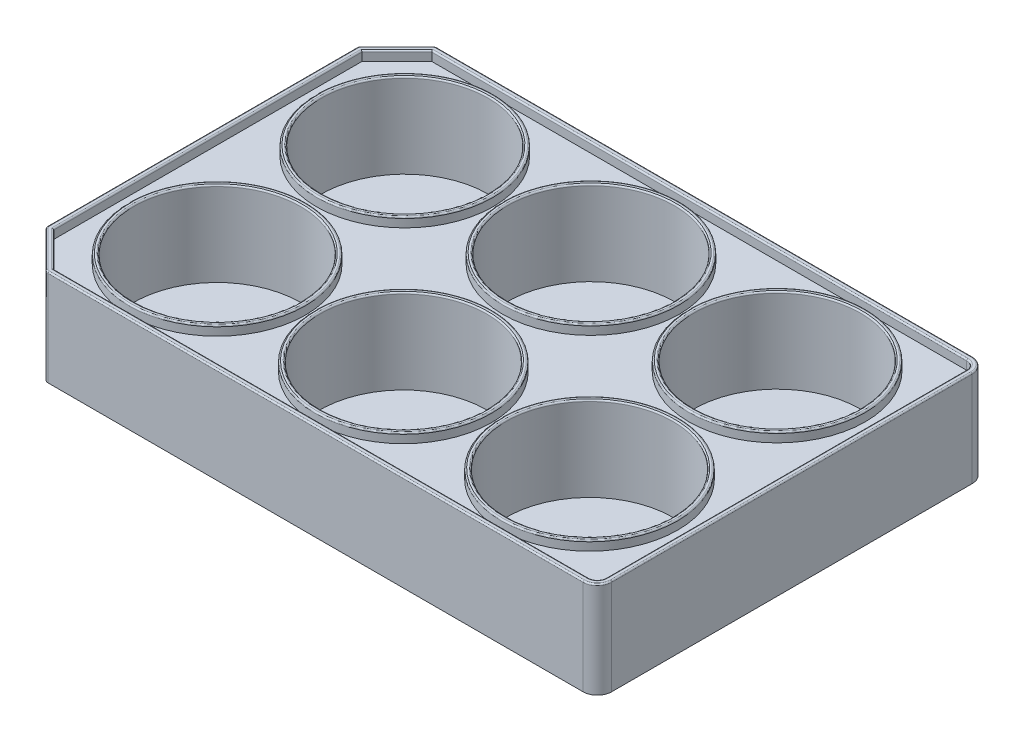
SolidWorks part; units mm, degrees
ref_plane "Front Plane" through (0, 0, 0) normal (0, 0, 1) x (1, 0, 0)
ref_plane "Top Plane" through (0, 0, 0) normal (0, 1, 0) x (1, 0, 0)
ref_plane "Right Plane" through (0, 0, 0) normal (1, 0, 0) x (0, 0, -1)
sketch "Sketch1" plane through (0, 0, 0) normal (0, 1, 0) x (1, 0, 0)
  line L1 (0, 0) -> (123.5, 0)
  line L2 (0, 0) -> (0, -81.5)
  line L3 (0, -81.5) -> (123.5, -81.5)
  line L4 (123.5, 0) -> (123.5, -81.5)
  dimension "D1" = 123.5
  dimension "D2" = 81.5
extrude "Boss-Extrude1" add sketch "Sketch1" along normal blind 20.16
chamfer "Chamfer1" distance 8 angle 45 2 edges at (0, 10.08, 0) (0, 10.08, 81.5)
fillet "Fillet1" radius 1 4 edges at (8, 10.08, 0) (0, 10.08, 8) (8, 10.08, 81.5) (0, 10.08, 73.5)
sketch "Sketch2" plane through (0, 20.16, 0) normal (0, 1, 0) x (1, 0, 0)
  line L0 (0, -8.4142) -> (0, -73.0858) construction
  line L1 (123.5, 0) -> (8.4142, 0) construction
  circle A0 centre (22.75, -21.1) radius 17.5
  circle A1 centre (61.75, -21.1) radius 17.5
  circle A2 centre (100.75, -21.1) radius 17.5
  circle A3 centre (61.75, -60.4) radius 17.5
  circle A4 centre (100.75, -60.4) radius 17.5
  circle A5 centre (22.75, -60.4) radius 17.5
  dimension "D2" = 35
  dimension "D3" = 21.1
  dimension "D1" = 22.75
  dimension "D4" = 3
  dimension "D5" = 2
extrude "Cut-Extrude1" cut sketch "Sketch2" against normal blind 17.7
fillet "Fillet2" radius 3 2 edges at (123.5, 10.08, 81.5) (123.5, 10.08, 0)
sketch "Sketch3" plane through (0, 20.16, 0) normal (0, 1, 0) x (1, 0, 0)
  line L0 (8.4763, -80.35) -> (120.5, -80.35)
  line L1 (122.35, -78.5) -> (122.35, -3)
  line L2 (120.5, -1.15) -> (8.4763, -1.15)
  line L3 (8.4763, -1.15) -> (1.15, -8.4763)
  line L4 (1.15, -8.4763) -> (1.15, -73.0237)
  line L5 (1.15, -73.0237) -> (8.4763, -80.35)
  line L6 (8.4142, -81.5) -> (120.5, -81.5)
  line L7 (123.5, -78.5) -> (123.5, -3)
  line L8 (120.5, 0) -> (8.4142, 0)
  line L9 (7.7071, -0.2929) -> (0.2929, -7.7071)
  line L10 (0, -8.4142) -> (0, -73.0858)
  line L11 (0.2929, -73.7929) -> (7.7071, -81.2071)
  line L12 (8.4142, -81.5) -> (120.5, -81.5) construction
  line L13 (123.5, -78.5) -> (123.5, -3) construction
  line L14 (120.5, 0) -> (8.4142, 0) construction
  line L15 (7.7071, -0.2929) -> (0.2929, -7.7071) construction
  line L16 (0, -8.4142) -> (0, -73.0858) construction
  line L17 (0.2929, -73.7929) -> (7.7071, -81.2071) construction
  arc A0 (120.5, -80.35) -> (122.35, -78.5) centre (120.5, -78.5) ccw
  arc A1 (122.35, -3) -> (120.5, -1.15) centre (120.5, -3) ccw
  arc A2 (8.4763, -1.15) -> (8.4763, -1.15) centre (8.4763, -1.15) ccw
  arc A3 (1.15, -8.4763) -> (1.15, -8.4763) centre (1.15, -8.4763) ccw
  arc A4 (1.15, -73.0237) -> (1.15, -73.0237) centre (1.15, -73.0237) ccw
  arc A5 (8.4763, -80.35) -> (8.4763, -80.35) centre (8.4763, -80.35) ccw
  arc A6 (120.5, -81.5) -> (123.5, -78.5) centre (120.5, -78.5) ccw
  arc A7 (123.5, -3) -> (120.5, 0) centre (120.5, -3) ccw
  arc A8 (8.4142, 0) -> (7.7071, -0.2929) centre (8.4142, -1) ccw
  arc A9 (0.2929, -7.7071) -> (0, -8.4142) centre (1, -8.4142) ccw
  arc A10 (0, -73.0858) -> (0.2929, -73.7929) centre (1, -73.0858) ccw
  arc A11 (7.7071, -81.2071) -> (8.4142, -81.5) centre (8.4142, -80.5) ccw
  arc A12 (120.5, -81.5) -> (123.5, -78.5) centre (120.5, -78.5) ccw construction
  arc A13 (123.5, -3) -> (120.5, 0) centre (120.5, -3) ccw construction
  arc A14 (8.4142, 0) -> (7.7071, -0.2929) centre (8.4142, -1) ccw construction
  arc A15 (0.2929, -7.7071) -> (0, -8.4142) centre (1, -8.4142) ccw construction
  arc A16 (0, -73.0858) -> (0.2929, -73.7929) centre (1, -73.0858) ccw construction
  arc A17 (7.7071, -81.2071) -> (8.4142, -81.5) centre (8.4142, -80.5) ccw construction
  circle A18 centre (22.75, -60.4) radius 17.5 construction
  circle A19 centre (61.75, -60.4) radius 17.5 construction
  circle A20 centre (100.75, -60.4) radius 17.5 construction
  circle A21 centre (100.75, -21.1) radius 17.5 construction
  circle A22 centre (61.75, -21.1) radius 17.5 construction
  circle A23 centre (22.75, -21.1) radius 17.5 construction
  circle A24 centre (22.75, -60.4) radius 17.5 construction
  circle A25 centre (61.75, -60.4) radius 17.5 construction
  circle A26 centre (100.75, -60.4) radius 17.5 construction
  circle A27 centre (100.75, -21.1) radius 17.5 construction
  circle A28 centre (61.75, -21.1) radius 17.5 construction
  circle A29 centre (22.75, -21.1) radius 17.5 construction
  circle A30 centre (22.75, -21.1) radius 18.5
  circle A31 centre (22.75, -60.4) radius 18.5
  circle A32 centre (61.75, -21.1) radius 18.5
  circle A33 centre (61.75, -60.4) radius 18.5
  circle A34 centre (100.75, -21.1) radius 18.5
  circle A35 centre (100.75, -60.4) radius 18.5
  dimension "D1" = 0
  dimension "D2" = 1.15
  dimension "D3" = 1
extrude "Cut-Extrude2" cut sketch "Sketch3" against normal blind 2
fillet "Fillet3" radius 0.3 32 edges at (22.75, 20.16, 39.6) (22.75, 20.16, 38.6) (61.75, 20.16, 39.6) (61.75, 20.16, 38.6) (100.75, 20.16, 39.6) (100.75, 20.16, 38.6) (100.75, 20.16, 78.9) (100.75, 20.16, 77.9) (61.75, 20.16, 78.9) (61.75, 20.16, 77.9) (22.75, 20.16, 78.9) (22.75, 20.16, 77.9) (8.0315, 20.16, 81.4239) (4, 20.16, 77.5) (0.0761, 20.16, 73.4685) (0, 20.16, 40.75) (0.0761, 20.16, 8.0315) (4, 20.16, 4) (8.0315, 20.16, 0.0761) (64.4571, 20.16, 0) (122.6213, 20.16, 0.8787) (123.5, 20.16, 40.75) (122.6213, 20.16, 80.6213) (64.4571, 20.16, 81.5) (64.4882, 20.16, 80.35) (121.8081, 20.16, 79.8081) (122.35, 20.16, 40.75) (121.8081, 20.16, 1.6919) (64.4882, 20.16, 1.15) (4.8132, 20.16, 4.8132) (1.15, 20.16, 40.75) (4.8132, 20.16, 76.6868)
